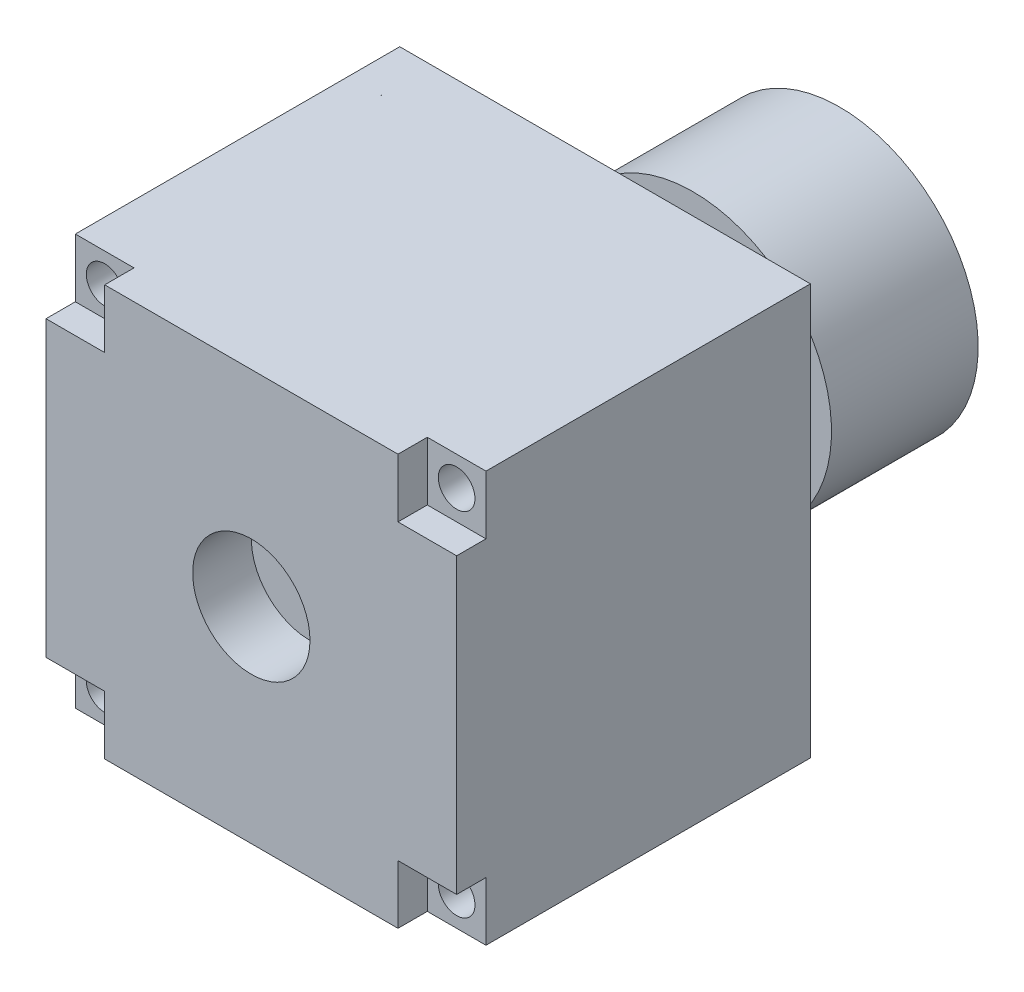
SolidWorks part; units mm, degrees
ref_plane "前视基准面" through (0, 0, 0) normal (0, 0, 1) x (1, 0, 0)
ref_plane "上视基准面" through (0, 0, 0) normal (0, 1, 0) x (1, 0, 0)
ref_plane "右视基准面" through (0, 0, 0) normal (1, 0, 0) x (0, 0, -1)
sketch "草图1" plane through (0, 0, 0) normal (0, 0, 1) x (1, 0, 0)
  line L1 (-14, -14) -> (14, -14)
  line L2 (-14, -14) -> (-14, 14)
  line L3 (-14, 14) -> (14, 14)
  line L4 (14, -14) -> (14, 14)
  line L5 (-14, -14) -> (14, 14) construction
  line L6 (-14, 14) -> (14, -14) construction
  point P0 (0, 0)
  dimension "D1" = 28
  dimension "D2" = 28
extrude "凸台-拉伸1" add sketch "草图1" along normal blind 24.12
sketch "草图2" plane through (0, 0, 24.12) normal (0, 0, 1) x (1, 0, 0)
  line L1 (-14, -14) -> (-10, -14)
  line L2 (-14, -14) -> (-14, -10)
  line L3 (-14, -10) -> (-10, -10)
  line L4 (-10, -14) -> (-10, -10)
  circle A0 centre (0, 0) radius 4
  dimension "D1" = 8
  dimension "D2" = 4
  dimension "D3" = 4
extrude "切除-拉伸1" cut sketch "草图2" against normal blind 2
sketch "草图3" plane through (0, 0, 22.12) normal (0, 0, 1) x (1, 0, 0)
  circle A0 centre (0, 0) radius 4
extrude "切除-拉伸2" cut sketch "草图3" against normal blind 2
hole_wizard "M3 螺纹孔2" positions "3D草图1" profile "草图6" tap size "M3" standard "GB" end condition up to next
sketch3d "3D草图1"
  line L0 (-14, -14, 22.12) -> (-10, -14, 22.12) construction
  line L1 (-14, -10, 22.12) -> (-14, -14, 22.12) construction
  point P0 (-12, -12, 22.12)
  dimension "D1" = 2
  dimension "D2" = 2
sketch "草图6" plane through (-12, -12, 22.12) normal (1, 0, 0) x (0, -1, 0)
  line L0 (0, 0) -> (0, 22.121)
  line L1 (0, 22.121) -> (1.25, 22.121)
  line L2 (1.25, 22.121) -> (1.25, 0)
  line L5 (1.25, 0) -> (0, 0)
  line L11 (0, -6.35) -> (0, 107.95) construction
  dimension "通孔螺纹孔钻头直径" = 2.5
  dimension "通孔螺纹孔钻头深度" = 22.121
cosmetic thread "孔螺蚊线2" parameters "D2"=3
pattern_circular "阵列(圆周)4" count 4 over 360 about axis through (0, 0, 0) along (0, 0, 1) of "切除-拉伸1"
pattern_circular "阵列(圆周)5" count 4 over 360 about axis through (0, 0, 0) along (0, 0, 1) of "M3 螺纹孔2"
sketch "草图7" plane through (0, 0, 0) normal (0, 0, -1) x (-1, 0, 0)
  circle A0 centre (0, 0) radius 2
  dimension "D1" = 4
extrude "凸台-拉伸2" add sketch "草图7" along normal blind 6
sketch "草图8" plane through (0, 0, -6) normal (0, 0, -1) x (-1, 0, 0)
  circle A0 centre (0, 0) radius 9.44
  circle A2 centre (0, 0) radius 4
  dimension "D1" = 18.88
  dimension "D2" = 8
extrude "凸台-拉伸3" add sketch "草图8" along normal blind 10 separate body
